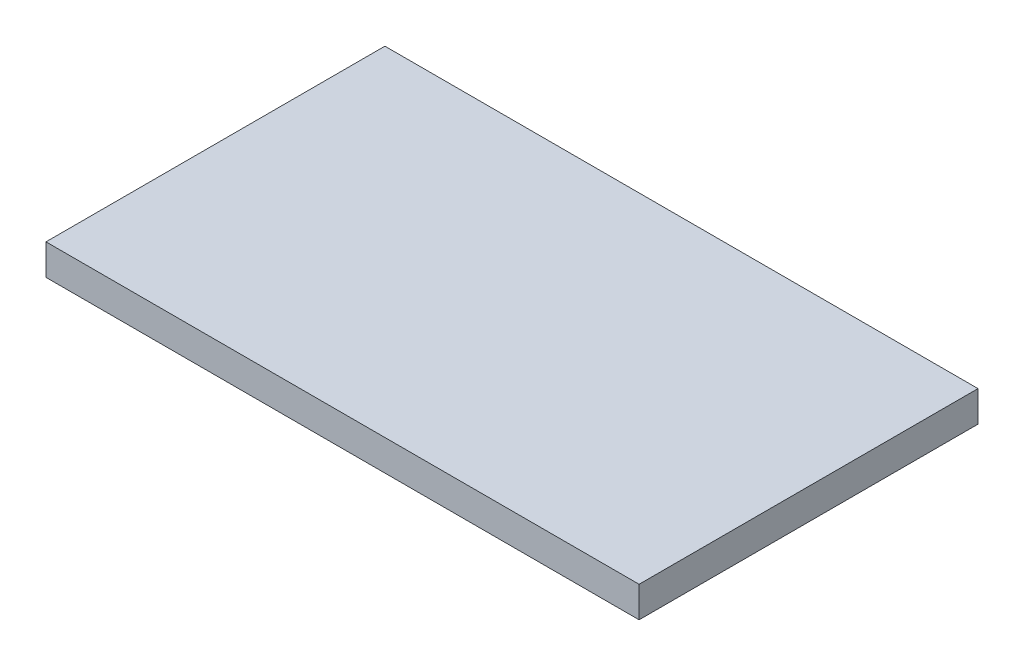
SolidWorks part; units mm, degrees
ref_plane "Front Plane" through (0, 0, 0) normal (0, 0, 1) x (1, 0, 0)
ref_plane "Top Plane" through (0, 0, 0) normal (0, 1, 0) x (1, 0, 0)
ref_plane "Right Plane" through (0, 0, 0) normal (1, 0, 0) x (0, 0, -1)
sketch "Sketch1" plane through (0, 0, 0) normal (0, 1, 0) x (1, 0, 0)
  line L1 (-19.25, -11) -> (19.25, -11)
  line L2 (-19.25, -11) -> (-19.25, 11)
  line L3 (-19.25, 11) -> (19.25, 11)
  line L4 (19.25, -11) -> (19.25, 11)
  line L5 (-19.25, -11) -> (19.25, 11) construction
  line L6 (-19.25, 11) -> (19.25, -11) construction
  point P0 (0, 0)
  dimension "D1" = 38.5
  dimension "D2" = 22
extrude "Boss-Extrude1" add sketch "Sketch1" along normal blind 2
